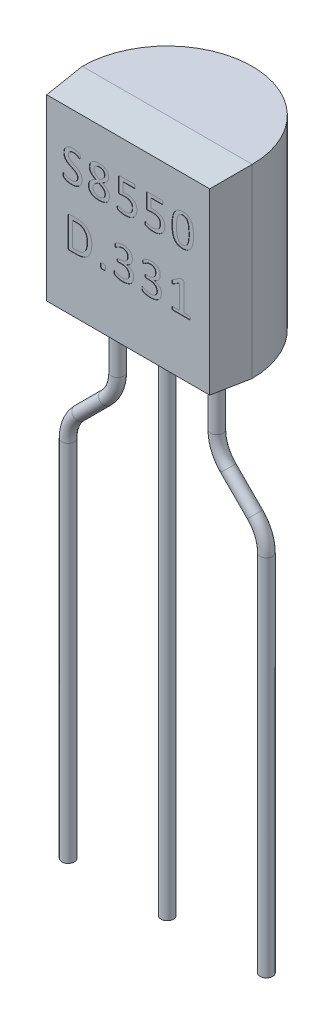
SolidWorks part; units mm, degrees
material "6061-T6 (SS)"
ref_plane "Front Plane" through (0, 0, 0) normal (0, 0, 1) x (1, 0, 0)
ref_plane "Top Plane" through (0, 0, 0) normal (0, 1, 0) x (1, 0, 0)
ref_plane "Right Plane" through (0, 0, 0) normal (1, 0, 0) x (0, 0, -1)
sketch "Sketch1" plane through (0, 0, 0) normal (0, 1, 0) x (1, 0, 0)
  line L0 (-2.175, 0) -> (2.175, 0)
  line L4 (0, 0) -> (0, -1.075) construction
  line L5 (0, 0) -> (0, 2.175) construction
  arc A0 (2.175, 0) -> (-2.175, 0) centre (0, 0) ccw
  dimension "D1" = 4.35
extrude "Boss-Extrude1" add sketch "Sketch1" along normal blind 4.75
sketch "Sketch2" plane through (0, 0, 0) normal (0, 0, 1) x (1, 0, 0)
  line L4 (-2.175, 0) -> (2.175, 0)
  line L5 (2.175, 0) -> (2.175, 4.75)
  line L6 (2.175, 4.75) -> (-2.175, 4.75)
  line L7 (-2.175, 4.75) -> (-2.175, 0)
  line L8 (-2.175, 0) -> (2.175, 0)
  line L9 (2.175, 0) -> (2.175, 4.75)
  line L10 (2.175, 4.75) -> (-2.175, 4.75)
  line L11 (-2.175, 4.75) -> (-2.175, 0)
  dimension "D1" = 0
extrude "Boss-Extrude2" add sketch "Sketch2" along normal blind 1 draft 5
sketch "Sketch3" plane through (0, 0, 1) normal (0, 0, 1) x (1, 0, 0)
  line L0 (0, 0) -> (0, 1.5) construction
  line L1 (0, 1.5) -> (0, 3) construction
  line L2 (-2.0875, 1.5) -> (2.0875, 1.5) construction
  line L3 (-2.0875, 4.6625) -> (-2.0875, 0.0875) construction
  line L4 (-2.0875, 3) -> (2.0875, 3) construction
  text T0 "S8550" font "Calibri" height 0.8
  text T1 "D.331" font "Calibri" height 0.8
  dimension "D1" = 1.5
  dimension "D2" = 3
extrude "Cut-Extrude1" cut sketch "Sketch3" against normal blind 0.01
sketch "Sketch4" plane through (0, 0, 0) normal (0, -1, 0) x (1, 0, 0)
  line L0 (-1.27, 0) -> (1.27, 0) construction
  circle A0 centre (0, 0) radius 0.16
  circle A1 centre (1.27, 0) radius 0.16
  circle A2 centre (-1.27, 0) radius 0.16
  dimension "D2" = 0.32
  dimension "D1" = 2.54
extrude "Boss-Extrude3" add sketch "Sketch4" along normal blind 1 and the other way blind 1 separate body
sketch "Sketch9" plane through (0, 0, 0) normal (0, 0, 1) x (1, 0, 0)
  line L0 (0.16, 1) -> (-0.16, 1) construction
  line L1 (-1.43, 1.5) -> (1.43, 1.5)
  line L2 (-1.43, 1.5) -> (-1.43, 0.5)
  line L3 (-1.43, 0.5) -> (1.43, 0.5)
  line L4 (1.43, 1.5) -> (1.43, 0.5)
  line L5 (-1.43, 1.5) -> (1.43, 0.5) construction
  line L6 (-1.43, 0.5) -> (1.43, 1.5) construction
  line L7 (-1.43, 1) -> (1.43, 1) construction
  point P0 (0, 1)
  dimension "D1" = 1
extrude "Boss-Extrude5" add sketch "Sketch9" along normal mid plane 0.2
sketch "Sketch6" plane through (0, -1, 0) normal (0, -1, 0) x (1, 0, 0)
  circle A1 centre (0, 0) radius 0.16
  circle A2 centre (0, 0) radius 0.16
  dimension "D1" = 0
extrude "Boss-Extrude4" add sketch "Sketch6" along normal blind 12
sketch "Sketch7" plane through (0, 0, 0) normal (0, 0, 1) x (1, 0, 0)
  line L0 (0, 0) -> (0, -13) construction
  line L1 (-0.16, -13) -> (0.16, -13) construction
  line L2 (-2.54, -13) -> (2.54, -13) construction
  line L3 (-2.54, -13) -> (-2.54, -3.6842)
  line L4 (-2.2471, -2.9771) -> (-1.5629, -2.2929)
  line L5 (-1.27, -1.5858) -> (-1.27, -1)
  line L6 (-1.43, -1) -> (-1.11, -1) construction
  line L7 (2.54, -13) -> (2.54, -3.6842) construction
  line L8 (2.2471, -2.9771) -> (1.5629, -2.2929) construction
  line L9 (1.27, -1.5858) -> (1.27, -1) construction
  line L10 (1.11, -1) -> (1.43, -1) construction
  line L11 (-1.27, -2) -> (0, -2) construction
  line L12 (0, -2) -> (1.27, -2) construction
  line L13 (-2.54, -3.27) -> (0, -3.27) construction
  line L14 (0, -3.27) -> (2.54, -3.27) construction
  arc A0 (-2.54, -3.6842) -> (-2.2471, -2.9771) centre (-1.54, -3.6842) cw
  arc A1 (-1.5629, -2.2929) -> (-1.27, -1.5858) centre (-2.27, -1.5858) ccw
  arc A2 (2.54, -3.6842) -> (2.2471, -2.9771) centre (1.54, -3.6842) ccw construction
  arc A3 (1.5629, -2.2929) -> (1.27, -1.5858) centre (2.27, -1.5858) cw construction
  dimension "D4" = 1
  dimension "D1" = 5.08
  dimension "D2" = 1
  dimension "D3" = 45
sketch "Sketch8" plane through (0, -1, 0) normal (0, -1, 0) x (1, 0, 0)
  circle A1 centre (-1.27, 0) radius 0.16
  circle A2 centre (-1.27, 0) radius 0.16
  dimension "D1" = 0
sweep "Sweep1" add profiles "Sketch8" path "Sketch7"
mirror "Mirror2" about plane through (0, 0, 0) normal (1, 0, 0) of "Sweep1"
